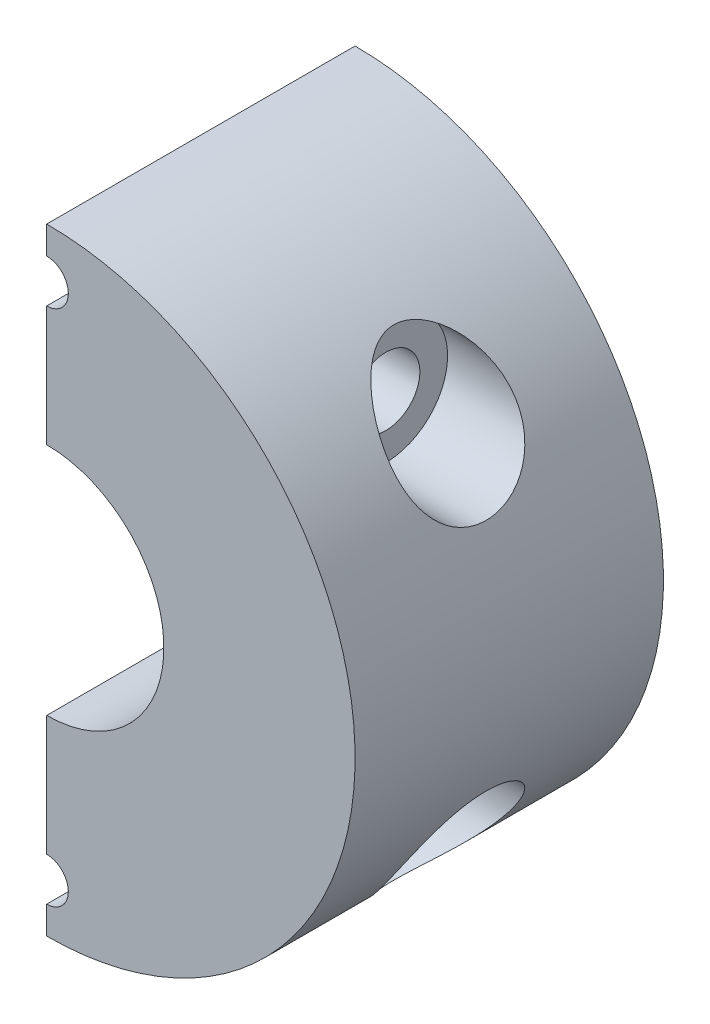
SolidWorks part; units mm, degrees
ref_plane "Front Plane" through (0, 0, 0) normal (0, 0, 1) x (1, 0, 0)
ref_plane "Top Plane" through (0, 0, 0) normal (0, 1, 0) x (1, 0, 0)
ref_plane "Right Plane" through (0, 0, 0) normal (1, 0, 0) x (0, 0, -1)
sketch "Sketch1" plane through (0, 0, 0) normal (0, 0, 1) x (1, 0, 0)
  circle A0 centre (0, 0) radius 25
  dimension "D1" = 50
extrude "Boss-Extrude1" add sketch "Sketch1" along normal blind 25
sketch "Sketch2" plane through (0, 0, 25) normal (0, 0, 1) x (1, 0, 0)
  circle A0 centre (0, 0) radius 9.5
  dimension "D1" = 19
extrude "Cut-Extrude1" cut sketch "Sketch2" against normal blind 20
sketch "Sketch3" plane through (0, 0, 5) normal (0, 0, 1) x (1, 0, 0)
  circle A0 centre (0, 0) radius 6
  dimension "D1" = 12
extrude "Cut-Extrude2" cut sketch "Sketch3" against normal blind 20
sketch "Sketch4" plane through (0, 0, 25) normal (0, 0, 1) x (1, 0, 0)
  line L1 (0, 25) -> (-31.9026, 25)
  line L2 (0, 25) -> (0, -25)
  line L3 (0, -25) -> (-31.9026, -25)
  line L4 (-31.9026, 25) -> (-31.9026, -25)
  circle A0 centre (0, 0) radius 25 construction
extrude "Cut-Extrude3" cut sketch "Sketch4" against normal through all
sketch "Sketch5" plane through (0, 0, 0) normal (-1, 0, 0) x (0, 0, 1)
  line L0 (0, -25) -> (0, -6) construction
  line L3 (5, -9.5) -> (25, -9.5) construction
  line L4 (0, 0) -> (25, 0) construction
  line L5 (25, -9.5) -> (25, 9.5) construction
  circle A0 centre (12.5, -14.5) radius 2.75
  circle A1 centre (12.5, 14.5) radius 2.75
  dimension "D1" = 5.5
  dimension "D2" = 12.5
  dimension "D3" = 5
extrude "Cut-Extrude4" cut sketch "Sketch5" against normal through all
sketch "Sketch6" plane through (0, 0, 0) normal (-1, 0, 0) x (0, 0, 1)
  circle A0 centre (12.5, 14.5) radius 5
  circle A1 centre (12.5, -14.5) radius 5
  dimension "D1" = 10
  dimension "D2" = 10
extrude "Cut-Extrude5" cut sketch "Sketch6" against normal blind 20 from offset 15 offset against normal yes
sketch "Sketch7" plane through (0, 0, 25) normal (0, 0, 1) x (1, 0, 0)
  line L0 (0, 9.5) -> (0, 25) construction
  line L1 (0, -25) -> (0, -9.5) construction
  circle A0 centre (0, 21) radius 1.75
  circle A1 centre (0, -21) radius 1.75
  dimension "D1" = 3.5
  dimension "D2" = 3.5
  dimension "D3" = 4
  dimension "D4" = 4
extrude "Cut-Extrude6" cut sketch "Sketch7" against normal through all
sketch "Sketch8" plane through (0, 0, 0) normal (0, 0, -1) x (-1, 0, 0)
  line L0 (0, 0) -> (-6, 0) construction
  circle A0 centre (0, 21) radius 3.5
  arc A1 (0, 6) -> (0, -6) centre (0, 0) ccw construction
  circle A2 centre (0, -21) radius 3.5
  dimension "D1" = 7
extrude "Cut-Extrude7" cut sketch "Sketch8" against normal blind 5
